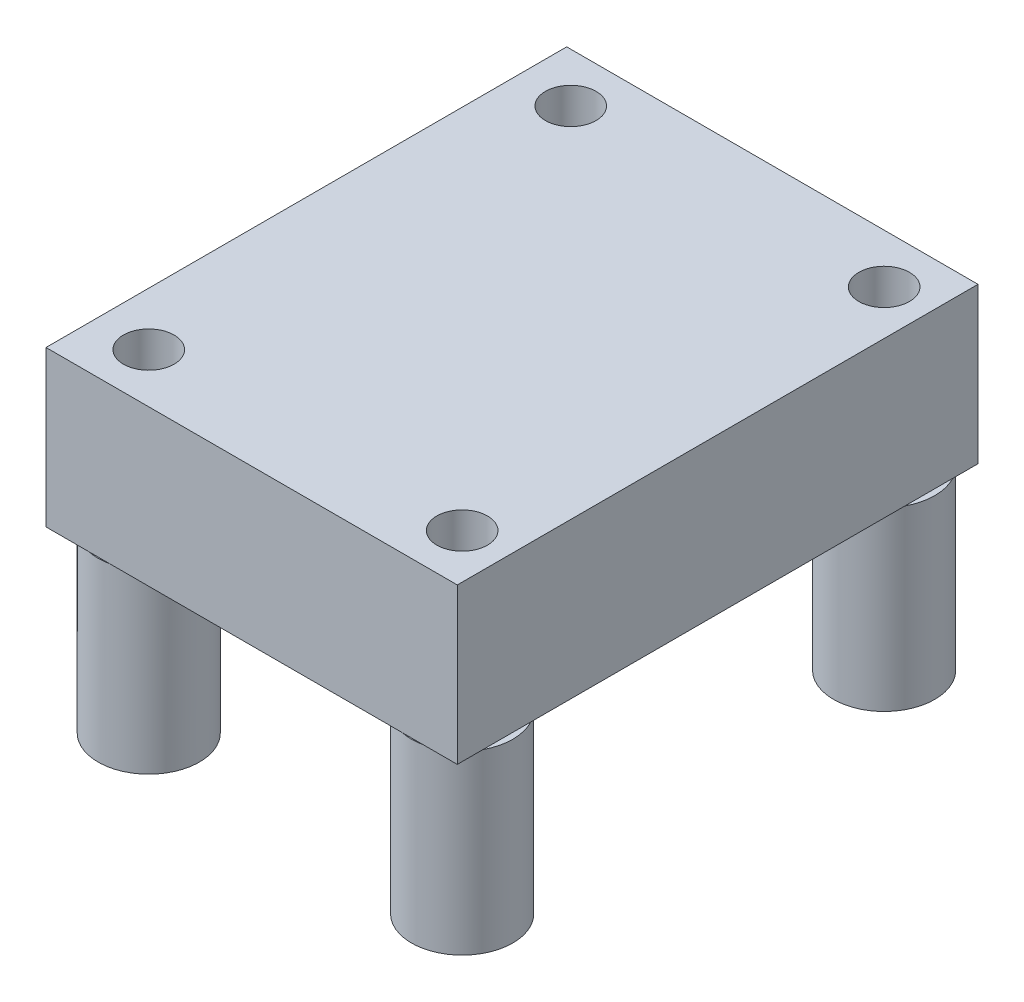
SolidWorks part; units mm, degrees
ref_plane "Front Plane" through (0, 0, 0) normal (0, 0, 1) x (1, 0, 0)
ref_plane "Top Plane" through (0, 0, 0) normal (0, 1, 0) x (1, 0, 0)
ref_plane "Right Plane" through (0, 0, 0) normal (1, 0, 0) x (0, 0, -1)
sketch "Sketch1" plane through (0, 0, 0) normal (0, 1, 0) x (1, 0, 0)
  line L1 (-9.1702, 8.063) -> (11.1298, 8.063)
  line L2 (-9.1702, 8.063) -> (-9.1702, -17.637)
  line L3 (-9.1702, -17.637) -> (11.1298, -17.637)
  line L4 (11.1298, 8.063) -> (11.1298, -17.637)
  dimension "D1" = 20.3
  dimension "D2" = 25.7
extrude "Boss-Extrude1" add sketch "Sketch1" along normal blind 7.6708
sketch "Sketch2" plane through (0, 0, 0) normal (0, -1, 0) x (-1, 0, 0)
  circle A0 centre (6.5435, -15.1921) radius 2.5
  circle A1 centre (-8.9251, -15.1921) radius 2.5
  circle A2 centre (-8.9251, 5.6359) radius 2.5
  circle A3 centre (6.5435, 5.6359) radius 2.5
  circle A4 centre (-8.9251, 5.6359) radius 1.25
  circle A5 centre (6.5435, 5.6359) radius 1.25
  circle A6 centre (-8.9251, -15.1921) radius 1.25
  circle A7 centre (6.5435, -15.1921) radius 1.25
  dimension "D1" = 5
  dimension "D2" = 2.5
  dimension "D3" = 5
  dimension "D4" = 2.5
  dimension "D5" = 2.5
  dimension "D6" = 5
  dimension "D7" = 2.5
  dimension "D8" = 5
  dimension "D9" = 20.828
  dimension "D10" = 20.828
  dimension "D11" = 15.4686
  dimension "D12" = 15.4686
extrude "Boss-Extrude2" add sketch "Sketch2" along normal blind 8.7122
sketch "Sketch3" plane through (0, 7.6708, 0) normal (0, 1, 0) x (1, 0, 0)
  circle A0 centre (8.9251, 5.6359) radius 1.25
  circle A1 centre (-6.5435, 5.6359) radius 1.25
  circle A2 centre (8.9251, -15.1921) radius 1.25
  circle A3 centre (-6.5435, -15.1921) radius 1.25
  dimension "D1" = 2.5
  dimension "D2" = 2.5
  dimension "D3" = 2.5
  dimension "D4" = 2.5
extrude "Cut-Extrude1" cut sketch "Sketch3" against normal through all both
